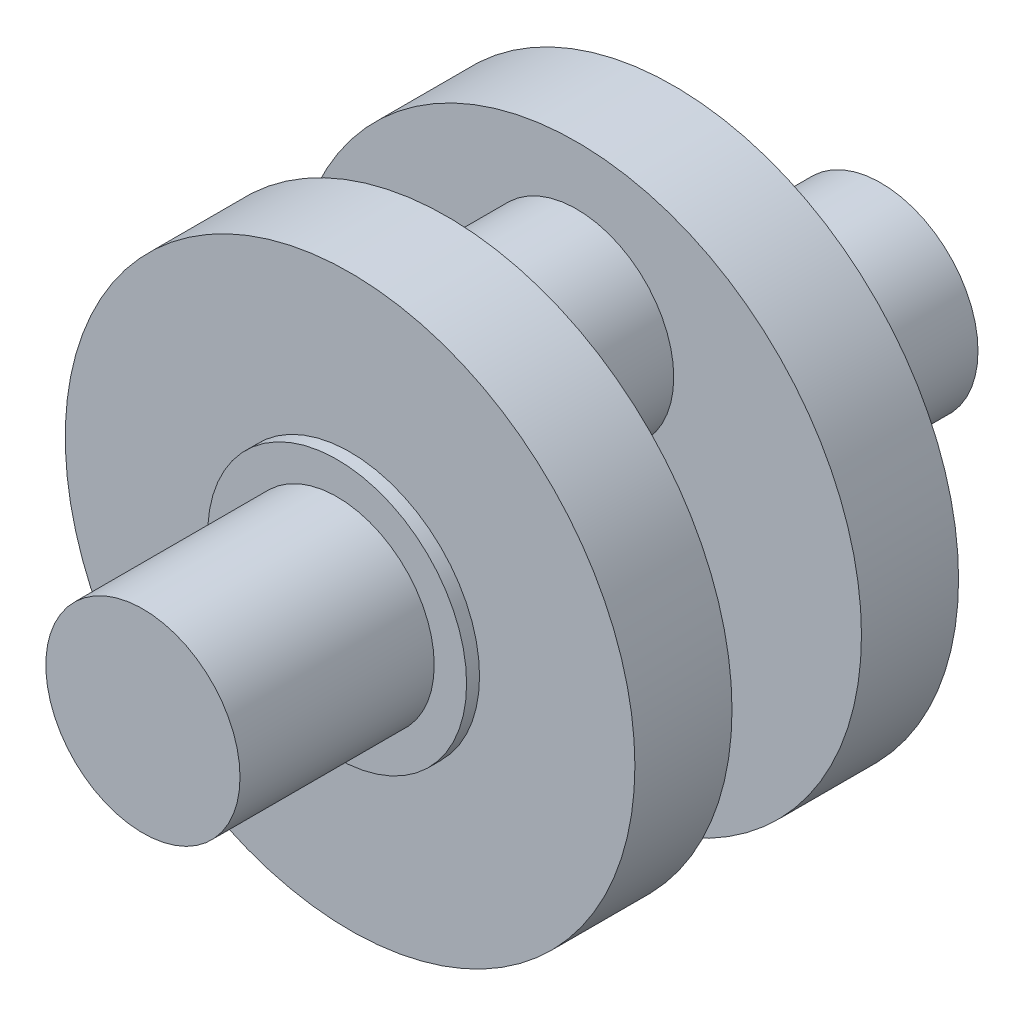
SolidWorks part; units mm, degrees
ref_plane "Płaszczyzna przednia" through (0, 0, 0) normal (0, 0, 1) x (1, 0, 0)
ref_plane "Płaszczyzna górna" through (0, 0, 0) normal (0, 1, 0) x (1, 0, 0)
ref_plane "Płaszczyzna prawa" through (0, 0, 0) normal (1, 0, 0) x (0, 0, -1)
sketch "Szkic1" plane through (0, 0, 0) normal (0, 0, 1) x (1, 0, 0)
  circle A0 centre (0, 0) radius 15
  dimension "D1" = 30
extrude "Dodanie-wyciągnięcie1" add sketch "Szkic1" along normal blind 30
sketch "Szkic2" plane through (0, 0, 0) normal (0, 0, 1) x (1, 0, 0)
  circle A0 centre (0, 0) radius 20
  dimension "D1" = 40
extrude "Dodanie-wyciągnięcie2" add sketch "Szkic2" against normal blind 2
sketch "Szkic3" plane through (0, 0, 0) normal (0, 0, 1) x (1, 0, 0)
  circle A0 centre (0, 0) radius 44
  dimension "D1" = 88
extrude "Dodanie-wyciągnięcie3" add sketch "Szkic3" against normal blind 15 from surface at -2 starting at face at (20, 0, -2)
sketch "Szkic4" plane through (0, 0, 0) normal (0, 0, 1) x (1, 0, 0)
  circle A0 centre (0, 20) radius 15
  point P2 (0, 0)
  dimension "D2" = 30
  dimension "D1" = 20
extrude "Dodanie-wyciągnięcie4" add sketch "Szkic4" against normal blind 10 from surface at -17 starting at face at (44, 0, -17)
mirror "Lustro2" about plane through (0, 20, -27) normal (0, 0, 1) of bodies 104
